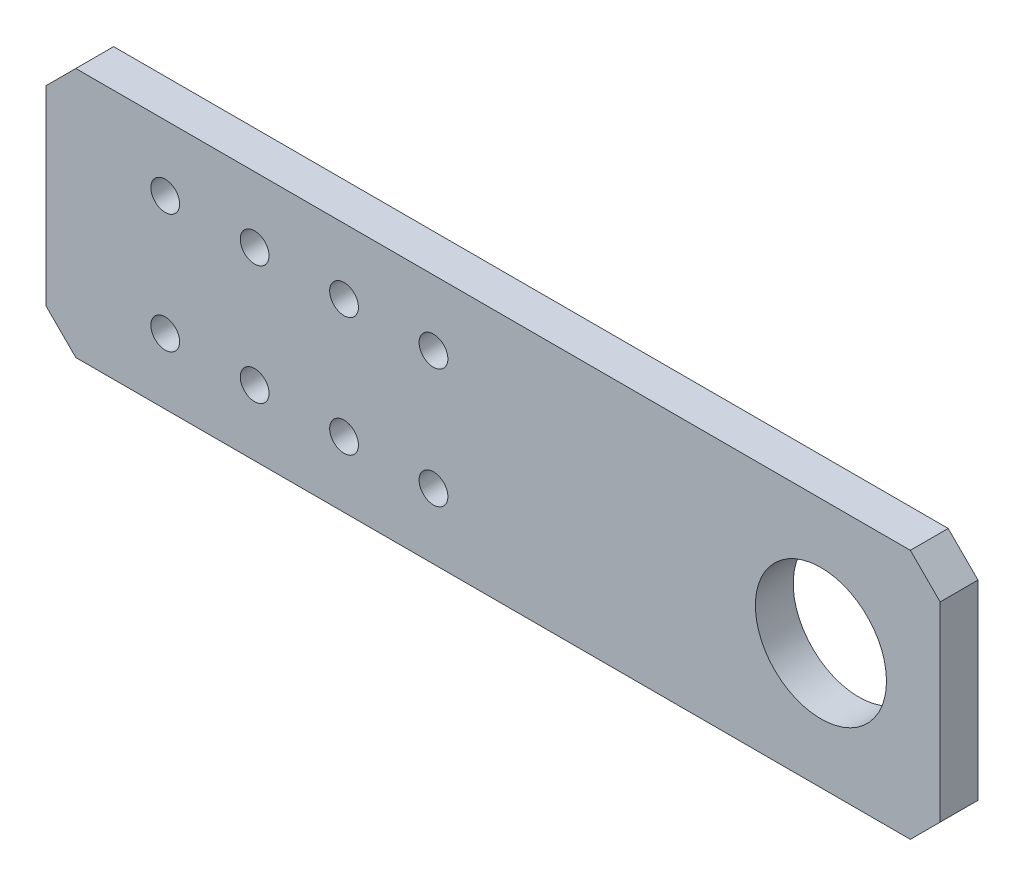
SolidWorks part; units mm, degrees
ref_plane "Front Plane" through (0, 0, 0) normal (0, 0, 1) x (1, 0, 0)
ref_plane "Top Plane" through (0, 0, 0) normal (0, 1, 0) x (1, 0, 0)
ref_plane "Right Plane" through (0, 0, 0) normal (1, 0, 0) x (0, 0, -1)
sketch "Sketch1" plane through (0, 0, 0) normal (0, 0, 1) x (1, 0, 0)
  line L1 (-102.5, 21) -> (102.5, 21)
  line L2 (-102.5, 21) -> (-102.5, -21)
  line L3 (-102.5, -21) -> (102.5, -21)
  line L4 (102.5, 21) -> (102.5, -21)
  line L5 (-102.5, 21) -> (102.5, -21) construction
  line L6 (-102.5, -21) -> (102.5, 21) construction
  point P0 (0, 0)
  dimension "D1" = 205
  dimension "D2" = 42
extrude "Boss-Extrude1" add sketch "Sketch1" along normal blind 6.35
sketch "Sketch3" plane through (0, 0, 6.35) normal (0, 0, 1) x (1, 0, 0)
  line L0 (-62.5, 10) -> (-62.5, -10) construction
  line L1 (-102.5, 21) -> (-102.5, -21) construction
  circle A0 centre (-62.5, 10) radius 2
  circle A1 centre (-62.5, -10) radius 2
  point P4 (-62.5, 0)
  dimension "D1" = 4
  dimension "D2" = 20
  dimension "D3" = 40
sketch "Sketch4" plane through (0, 0, 6.35) normal (0, 0, 1) x (1, 0, 0)
  line L0 (-102.5, 21) -> (-102.5, -21) construction
  line L1 (102.5, -21) -> (102.5, 21) construction
  circle A0 centre (-78.5, 0) radius 11
  circle A1 centre (82.5, 0) radius 11 construction
  dimension "D2" = 22
  dimension "D3" = 20
  dimension "D1" = 24
  dimension "D4" = 161
extrude "Cut-Extrude3" cut sketch "Sketch4" against normal through all
chamfer "Chamfer1" distance 5 angle 45 4 edges at (-102.5, 21, 3.175) (-102.5, -21, 3.175) (102.5, 21, 3.175) (102.5, -21, 3.175)
sketch "Sketch5" [suppressed] plane through (0, 0, 6.35) normal (0, 0, 1) x (1, 0, 0)
  line L0 (100, -16) -> (100, 16) construction
  circle A0 centre (77, 0) radius 11
  dimension "D1" = 22
  dimension "D2" = 23
extrude "Cut-Extrude4" [suppressed] cut sketch "Sketch5" against normal blind 25
sketch "Sketch7" plane through (0, 0, 6.35) normal (0, 0, 1) x (1, 0, 0)
  line L4 (7.5, 3.175) -> (-7.5, 3.175)
  line L5 (7.5, -3.175) -> (7.5, 3.175)
  line L6 (-7.5, -3.175) -> (7.5, -3.175)
  line L7 (-7.5, 3.175) -> (-7.5, -3.175)
  line L8 (7.5, 3.175) -> (-7.5, 3.175)
  line L9 (7.5, -3.175) -> (7.5, 3.175)
  line L10 (-7.5, -3.175) -> (7.5, -3.175)
  line L11 (-7.5, 3.175) -> (-7.5, -3.175)
  dimension "D1" = 0
sketch "Sketch8" plane through (0, 0, 6.35) normal (0, 0, 1) x (1, 0, 0)
  line L4 (25.5, 3.175) -> (10.5, 3.175)
  line L5 (10.5, 3.175) -> (10.5, -3.175)
  line L6 (10.5, -3.175) -> (25.5, -3.175)
  line L7 (25.5, -3.175) -> (25.5, 3.175)
  line L8 (25.5, 3.175) -> (10.5, 3.175)
  line L9 (10.5, 3.175) -> (10.5, -3.175)
  line L10 (10.5, -3.175) -> (25.5, -3.175)
  line L11 (25.5, -3.175) -> (25.5, 3.175)
  dimension "D1" = 0
extrude "Cut-Extrude7" [suppressed] cut sketch "Sketch8" against normal through all
sketch "Sketch9" plane through (0, 0, 6.35) normal (0, 0, 1) x (1, 0, 0)
  circle A0 centre (82.5, 0) radius 11 construction
  circle A1 centre (82.5, 0) radius 11
extrude "Cut-Extrude8" cut sketch "Sketch9" against normal through all
sketch "Sketch10" [suppressed] plane through (0, 0, 6.35) normal (0, 0, 1) x (1, 0, 0)
  circle A0 centre (80, 0) radius 15
  dimension "D1" = 25
extrude "Cut-Extrude9" [suppressed] cut sketch "Sketch10" against normal through all
sketch "Sketch11" plane through (0, 0, 6.35) normal (0, 0, 1) x (1, 0, 0)
  circle A0 centre (95.5563, 15.5563) radius 1.5 construction
  circle A1 centre (64.4437, 15.5563) radius 1.5 construction
  circle A2 centre (95.5563, -15.5563) radius 1.5 construction
  circle A3 centre (64.4437, -15.5563) radius 1.5 construction
  circle A4 centre (95.5563, 15.5563) radius 1.5
  circle A5 centre (64.4437, 15.5563) radius 1.5
  circle A6 centre (95.5563, -15.5563) radius 1.5
  circle A7 centre (64.4437, -15.5563) radius 1.5
sketch "Sketch12" plane through (0, 0, 6.35) normal (0, 0, 1) x (1, 0, 0)
  line L0 (-102.5, 16) -> (-102.5, -16) construction
  circle A0 centre (-95.5, 0) radius 3.302
  point P4 (-102.5, 0)
  dimension "D1" = 6.604
  dimension "D2" = 7
sketch "Sketch14" plane through (0, 0, 6.35) normal (0, 0, 1) x (1, 0, 0)
  line L0 (-47.5, 16) -> (-47.5, -16)
  line L1 (97.5, 21) -> (-97.5, 21) construction
  line L2 (-97.5, -21) -> (97.5, -21) construction
  line L3 (102.5, -16) -> (102.5, 16) construction
  line L4 (-42.5, 21) -> (-47.5, 16)
  line L13 (-47.5, -16) -> (-42.5, -21)
  line L14 (97.5, 21) -> (-97.5, 21)
  line L15 (-97.5, -21) -> (97.5, -21)
  line L16 (0, 0) -> (-47.5, 0) construction
  line L20 (97.5, 21) -> (-97.5, 21)
  line L21 (-97.5, 21) -> (-102.5, 16)
  line L22 (-102.5, 16) -> (-102.5, -16)
  line L23 (-102.5, -16) -> (-97.5, -21)
  line L24 (-97.5, -21) -> (97.5, -21)
  line L25 (97.5, -21) -> (102.5, -16)
  line L26 (102.5, -16) -> (102.5, 16)
  line L27 (102.5, 16) -> (97.5, 21)
  line L28 (97.5, 21) -> (-42.5, 21)
  line L29 (-97.5, 21) -> (-102.5, 16)
  line L30 (-102.5, 16) -> (-102.5, -16)
  line L31 (-102.5, -16) -> (-97.5, -21)
  line L32 (-42.5, -21) -> (97.5, -21)
  line L33 (97.5, -21) -> (102.5, -16)
  line L34 (102.5, -16) -> (102.5, 16)
  line L35 (102.5, 16) -> (97.5, 21)
  circle A4 centre (-27.5, 10) radius 2.413
  circle A5 centre (-12.5, 10) radius 2.413
  circle A6 centre (-12.5, -10) radius 2.413
  circle A7 centre (-27.5, -10) radius 2.413
  circle A8 centre (17.5, 10) radius 2.413
  circle A9 centre (2.5, 10) radius 2.413
  circle A10 centre (17.5, -10) radius 2.413
  circle A11 centre (2.5, -10) radius 2.413
  point P0 (-47.5, 21)
  point P1 (-47.5, -21)
  circle M14 centre (-78.5, 0) radius 11
  line M15 (97.5, 21) -> (-97.5, 21)
  line M16 (-97.5, 21) -> (-102.5, 16)
  line M17 (-102.5, 16) -> (-102.5, -16)
  line M18 (-102.5, -16) -> (-97.5, -21)
  line M19 (-97.5, -21) -> (97.5, -21)
  dimension "D7" = 20
  dimension "D3" = 4.826
  dimension "D1" = 150
  dimension "D2" = 0
  dimension "D4" = 15
  dimension "D8" = 10
  dimension "D9" = 2
extrude "Cut-Extrude10" cut sketch "Sketch14" against normal blind 10 contours L13 L0 L4 M15 M16 M17 M18 M19 M14 | A4 | A7 | A6 | A5 | A8 | A11 | A10 | A9
